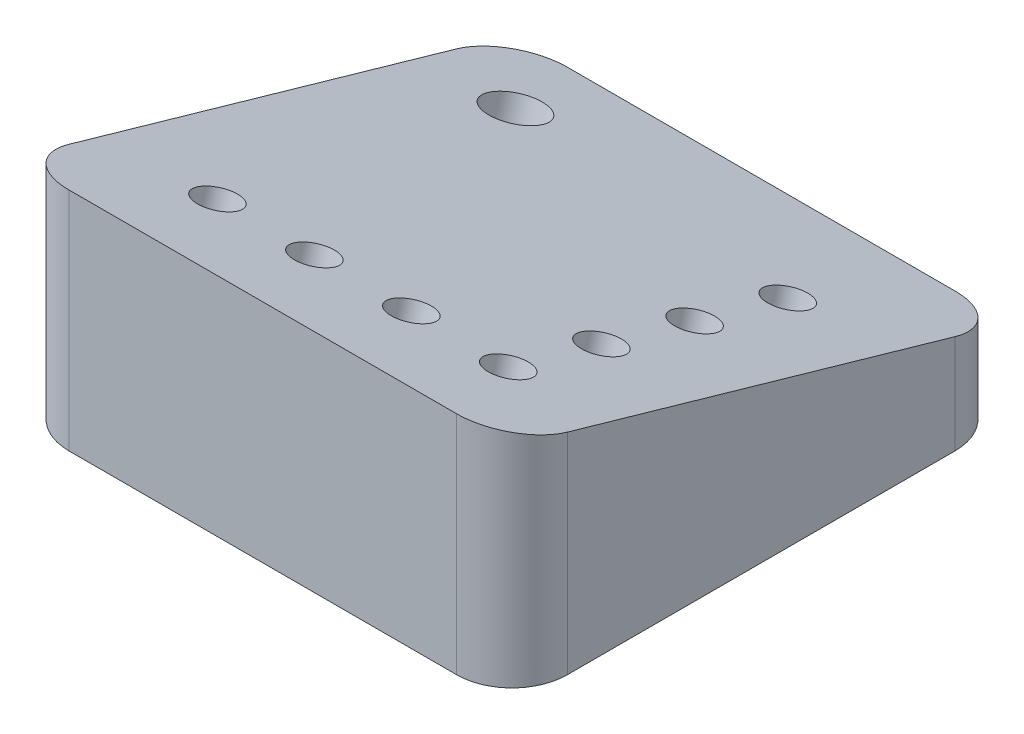
SolidWorks part; units mm, degrees
material "6061 Alloy"
ref_plane "Alzado" through (0, 0, 0) normal (0, 0, 1) x (1, 0, 0)
ref_plane "Planta" through (0, 0, 0) normal (0, 1, 0) x (1, 0, 0)
ref_plane "Vista lateral" through (0, 0, 0) normal (1, 0, 0) x (0, 0, -1)
sketch "Sketch2" plane through (0, 0, 0) normal (1, 0, 0) x (0, 0, -1)
  line L0 (37.2355, 0) -> (37.2355, 12)
  line L1 (-34.7645, 0) -> (37.2355, 0)
  line L2 (37.2355, 12) -> (-34.7645, 32.6457)
  line L3 (-34.7645, 32.6457) -> (-34.7645, 0)
  dimension "D1" = 72
  dimension "D2" = 16
  dimension "D3" = 12
extrude "Boss-Extrude1" add sketch "Sketch2" along normal mid plane 72
fillet "Fillet2" radius 8 4 edges at (-36, 6, -37.2355) (36, 6, -37.2355) (-36, 16.3228, 34.7645) (36, 16.3228, 34.7645)
sketch "Sketch3" plane through (0, 20.9542, -6.0085) normal (0, 0.9613, -0.2756) x (1, 0, 0)
  line L2 (-20, -28.4162) -> (22, -28.4162) construction
  line L3 (22, -28.4162) -> (22, 13.5838) construction
  line L4 (28, -42.4162) -> (-28, -42.4162) construction
  line L5 (36, 24.163) -> (36, -34.0938) construction
  circle A1 centre (-20, -28.4162) radius 3
  circle A2 centre (-6, -28.4162) radius 3
  circle A3 centre (8, -28.4162) radius 3
  circle A4 centre (22, -28.4162) radius 3
  circle A5 centre (22, -14.4162) radius 3
  circle A6 centre (22, -0.4162) radius 3
  circle A7 centre (22, 13.5838) radius 3
  point P26 (34.0754, 7.4775)
  dimension "D3" = 14
  dimension "D7" = 6
  dimension "14" = 14
  dimension "D4" = 14
  dimension "D5" = 14
  dimension "D6" = 14
  dimension "D8" = 14
  dimension "D9" = 14
  dimension "D10" = 14
sketch "Sketch4" plane through (0, 20.9542, -6.0085) normal (0, 0.9613, -0.2756) x (1, 0, 0)
  line L0 (28, 32.4854) -> (-28, 32.4854) construction
  line L1 (-36, 24.163) -> (-36, -34.0938) construction
  circle A0 centre (-23, 19.4854) radius 4
  point P6 (-36, 12.4403)
  point P9 (-38.179, 62.9177)
  dimension "D1" = 8
  dimension "D2" = 13
  dimension "D3" = 13
extrude "Cut-Extrude2" cut sketch "Sketch4" against normal through all
extrude "Cut-Extrude3" cut sketch "Sketch3" against normal blind 12
